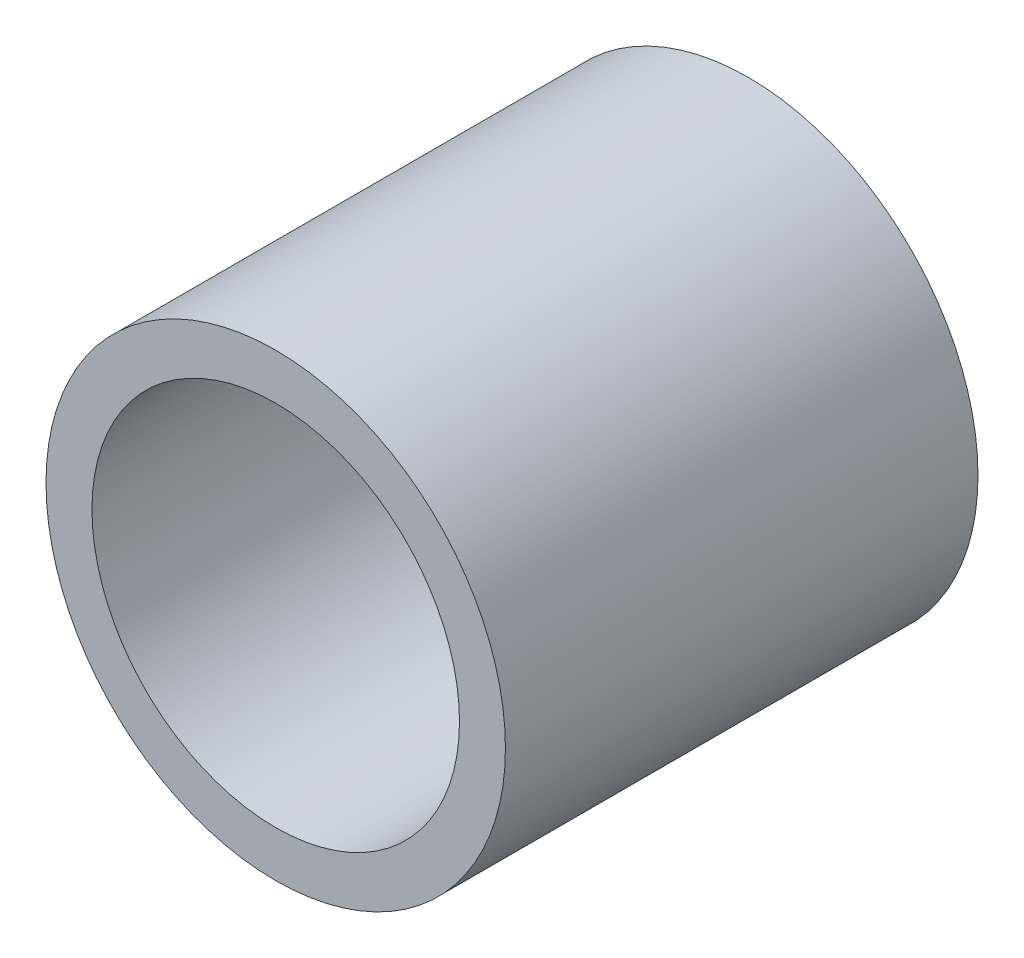
SolidWorks part; units mm, degrees
ref_plane "Front Plane" through (0, 0, 0) normal (0, 0, 1) x (1, 0, 0)
ref_plane "Top Plane" through (0, 0, 0) normal (0, 1, 0) x (1, 0, 0)
ref_plane "Right Plane" through (0, 0, 0) normal (1, 0, 0) x (0, 0, -1)
sketch "Sketch2" plane through (0, 0, 0) normal (0, 0, 1) x (1, 0, 0)
  circle A0 centre (0, 0) radius 14
  circle A1 centre (0, 0) radius 17.5
  dimension "D1" = 28
  dimension "D2" = 35
extrude "Boss-Extrude1" add sketch "Sketch2" along normal blind 36
